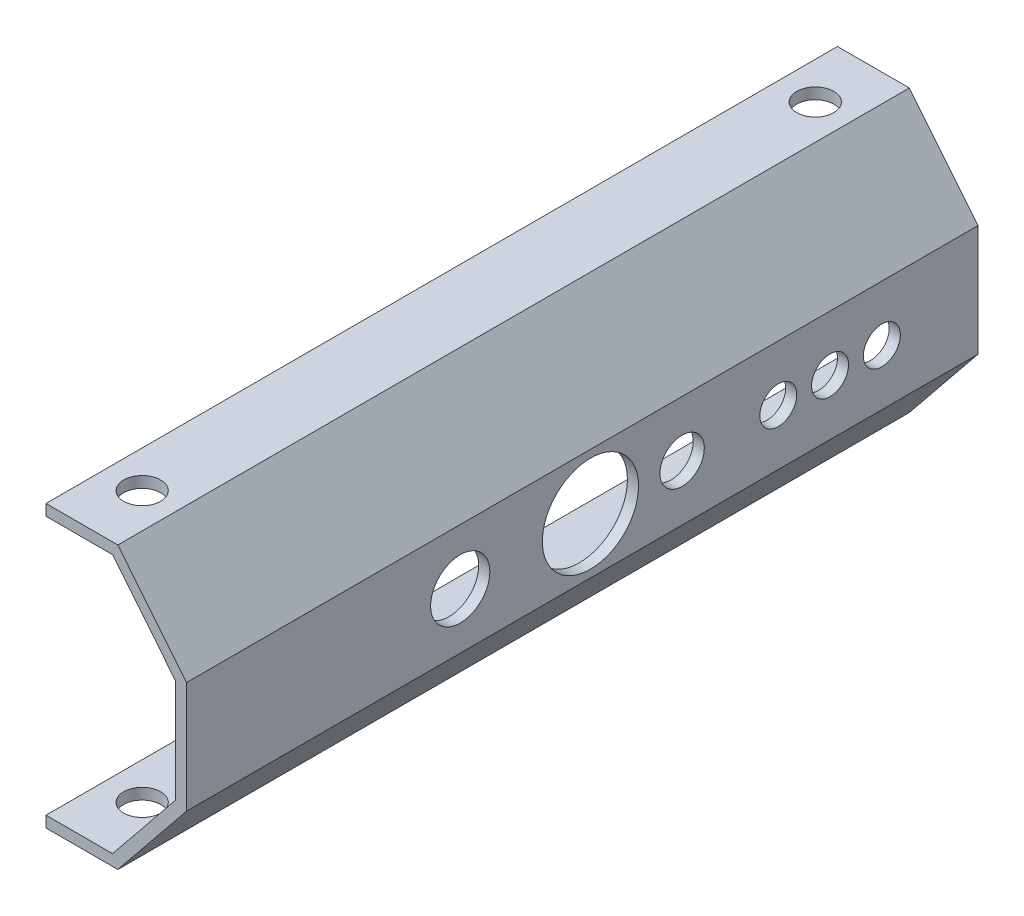
SolidWorks part; units mm, degrees
ref_plane "Alzado" through (0, 0, 0) normal (0, 0, 1) x (1, 0, 0)
ref_plane "Planta" through (0, 0, 0) normal (0, 1, 0) x (1, 0, 0)
ref_plane "Vista lateral" through (0, 0, 0) normal (1, 0, 0) x (0, 0, -1)
sketch "Croquis1" plane through (0, 0, 0) normal (0, 0, 1) x (1, 0, 0)
  line L0 (0, 0) -> (9, 0)
  line L1 (17.5, 17.5) -> (-30.8706, 17.5) construction
  line L2 (17.5, 10.5) -> (17.5, 24.5)
  line L3 (9, 0) -> (17.5, 10.5)
  line L4 (0, 35) -> (9, 35)
  line L5 (9, 35) -> (17.5, 24.5)
  line L6 (0, -1.5) -> (9.7156, -1.5)
  line L7 (9.7156, -1.5) -> (19, 9.969)
  line L8 (19, 9.969) -> (19, 25.031)
  line L9 (9.7156, 36.5) -> (19, 25.031)
  line L10 (0, 36.5) -> (9.7156, 36.5)
  line L11 (0, 0) -> (0, -1.5)
  line L12 (0, 36.5) -> (0, 35)
  dimension "D1" = 9
  dimension "D2" = 14
  dimension "D3" = 35
  dimension "D5" = 19
  dimension "D4" = 1.5
extrude "Saliente-Extruir1" add sketch "Croquis1" along normal blind 107
sketch "Croquis3" plane through (0, 36.5, 0) normal (0, 1, 0) x (1, 0, 0)
  line L0 (9.7156, 0) -> (0, 0) construction
  line L1 (9, -107) -> (9, 0) construction
  line L2 (9.7156, -53.5) -> (0, -53.5) construction
  line L3 (9.7156, -107) -> (9.7156, 0) construction
  line L4 (0, -107) -> (0, 0) construction
  circle A0 centre (5, -8) radius 2.5
  circle A1 centre (5, -99) radius 2.5
  dimension "D1" = 5
  dimension "D2" = 8
  dimension "D3" = 4
extrude "Cortar-Extruir1" cut sketch "Croquis3" against normal up to next
sketch "Croquis4" plane through (0, -1.5, 0) normal (0, -1, 0) x (1, 0, 0)
  line L0 (0, 0) -> (9.7156, 0) construction
  line L1 (9, 107) -> (9, 0) construction
  line L2 (9.7156, 53.5) -> (0, 53.5) construction
  line L3 (9.7156, 107) -> (9.7156, 0) construction
  line L4 (0, 107) -> (0, 0) construction
  circle A0 centre (5, 8) radius 2.5
  circle A1 centre (5, 99) radius 2.5
  dimension "D1" = 5
  dimension "D2" = 8
  dimension "D3" = 4
extrude "Cortar-Extruir2" cut sketch "Croquis4" against normal up to next
sketch "Croquis5" plane through (19, 0, 0) normal (1, 0, 0) x (0, 0, -1)
  line L4 (0, 9.969) -> (0, 25.031) construction
  circle A0 centre (-40, 17.5) radius 3
  circle A1 centre (-70, 17.5) radius 4
  dimension "D1" = 6
  dimension "D2" = 8
  dimension "D3" = 70
  dimension "D4" = 40
extrude "Cortar-Extruir3" cut sketch "Croquis5" against normal up to next contours A0 | A1
sketch "Croquis6" plane through (19, 0, 0) normal (1, 0, 0) x (0, 0, -1)
  line L2 (-107, 25.031) -> (0, 25.031) construction
  circle A0 centre (-52.3957, 17.501) radius 6.5
  point P6 (-45.646, 9.969)
  dimension "D1" = 13
  dimension "D2" = 7.53
extrude "Cortar-Extruir4" cut sketch "Croquis6" against normal up to next
sketch "Croquis7" plane through (19, 0, 0) normal (1, 0, 0) x (0, 0, -1)
  line L0 (-107, 9.969) -> (0, 9.969) construction
  circle A0 centre (-27, 17.504) radius 2.5
  circle A1 centre (-20, 17.504) radius 2.5
  circle A2 centre (-13, 17.504) radius 2.5
  circle A3 centre (-40, 17.5) radius 3 construction
  dimension "D1" = 5
  dimension "D2" = 5
  dimension "D3" = 5
  dimension "D7" = 13
  dimension "D4" = 7
  dimension "D5" = 7
  dimension "D6" = 7.535
extrude "Cortar-Extruir5" cut sketch "Croquis7" against normal up to next
